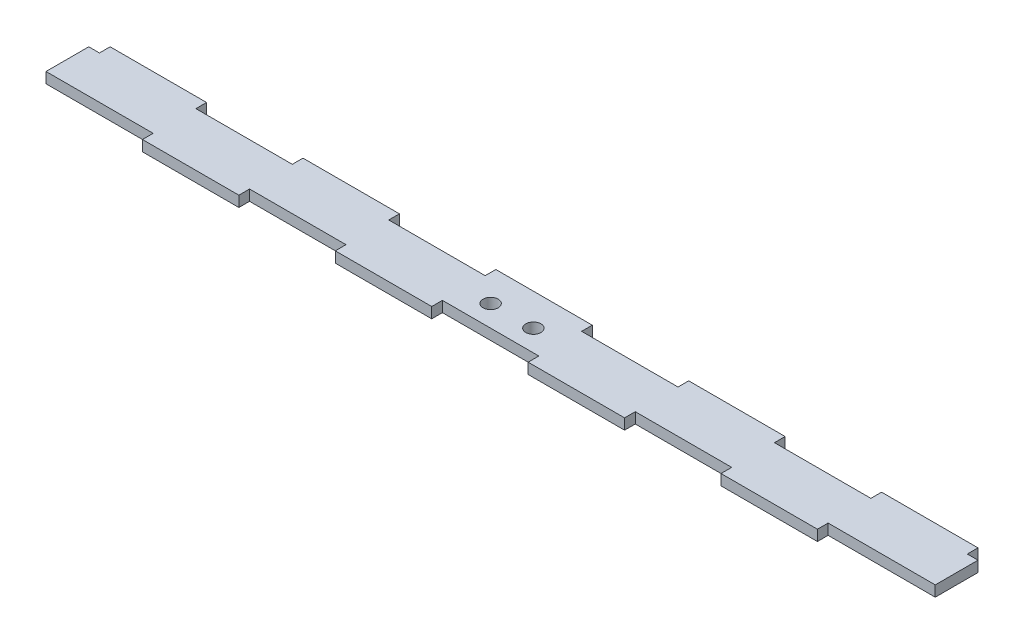
SolidWorks part; units mm, degrees
ref_plane "Front Plane" through (0, 0, 0) normal (0, 0, 1) x (1, 0, 0)
ref_plane "Top Plane" through (0, 0, 0) normal (0, 1, 0) x (1, 0, 0)
ref_plane "Right Plane" through (0, 0, 0) normal (1, 0, 0) x (0, 0, -1)
sketch "Sketch1" plane through (0, 0, 0) normal (0, 1, 0) x (1, 0, 0)
  line L0 (-128.905, 9.525) -> (-100.2594, 9.525)
  line L1 (-100.2594, 9.525) -> (-100.2594, 6.35)
  line L2 (-100.2594, 6.35) -> (-71.6139, 6.35)
  line L3 (-71.6139, 6.35) -> (-71.6139, 9.525)
  line L4 (-71.6139, 9.525) -> (-42.9683, 9.525)
  line L5 (-128.905, 9.525) -> (-128.905, 6.35)
  line L6 (-128.905, 6.35) -> (-132.08, 6.35)
  line L7 (-132.08, 6.35) -> (-132.08, -6.35)
  line L10 (-132.08, -6.35) -> (-100.2594, -6.35)
  line L11 (-100.2594, -6.35) -> (-100.2594, -9.525)
  line L12 (-100.2594, -9.525) -> (-71.6139, -9.525)
  line L13 (-71.6139, -9.525) -> (-71.6139, -6.35)
  line L14 (-71.6139, -6.35) -> (-42.9683, -6.35)
  line L15 (-42.9683, 9.525) -> (-42.9683, 6.35)
  line L16 (-42.9683, 6.35) -> (-14.3228, 6.35)
  line L17 (-14.3228, 6.35) -> (-14.3228, 9.525)
  line L18 (-14.3228, 9.525) -> (14.3228, 9.525)
  line L19 (14.3228, 9.525) -> (14.3228, 6.35)
  line L20 (14.3228, 6.35) -> (42.9683, 6.35)
  line L21 (42.9683, 6.35) -> (42.9683, 9.525)
  line L22 (42.9683, 9.525) -> (71.6139, 9.525)
  line L23 (71.6139, 9.525) -> (71.6139, 6.35)
  line L24 (71.6139, 6.35) -> (100.2594, 6.35)
  line L25 (100.2594, 6.35) -> (100.2594, 9.525)
  line L26 (100.2594, 9.525) -> (128.905, 9.525)
  line L27 (128.905, 9.525) -> (128.905, 6.35)
  line L28 (128.905, 6.35) -> (132.08, 6.35)
  line L29 (132.08, 6.35) -> (132.08, -6.35)
  line L32 (132.08, -6.35) -> (100.2594, -6.35)
  line L33 (100.2594, -6.35) -> (100.2594, -9.525)
  line L34 (100.2594, -9.525) -> (71.6139, -9.525)
  line L35 (71.6139, -9.525) -> (71.6139, -6.35)
  line L36 (71.6139, -6.35) -> (42.9683, -6.35)
  line L37 (42.9683, -6.35) -> (42.9683, -9.525)
  line L38 (42.9683, -9.525) -> (14.3228, -9.525)
  line L39 (14.3228, -9.525) -> (14.3228, -6.35)
  line L40 (14.3228, -6.35) -> (-14.3228, -6.35)
  line L41 (-14.3228, -6.35) -> (-14.3228, -9.525)
  line L42 (-14.3228, -9.525) -> (-42.9683, -9.525)
  line L43 (-42.9683, -9.525) -> (-42.9683, -6.35)
  line L44 (-132.08, 0) -> (132.08, 0) construction
  line L45 (-6.35, 0) -> (0, 0) construction
  line L46 (0, 0) -> (6.35, 0) construction
  circle A0 centre (6.35, 0) radius 2.25
  circle A1 centre (-6.35, 0) radius 2.25
  point P16 (-132.08, 0)
  point P41 (0, 0)
  point P47 (-12.7, 0)
  dimension "D6" = 4.5
  dimension "D1" = 19.05
  dimension "D2" = 3.175
  dimension "D3" = 264.16
  dimension "D4" = 15.875
  dimension "D5" = 12.7
extrude "Boss-Extrude2" add sketch "Sketch1" along normal blind 3.175
